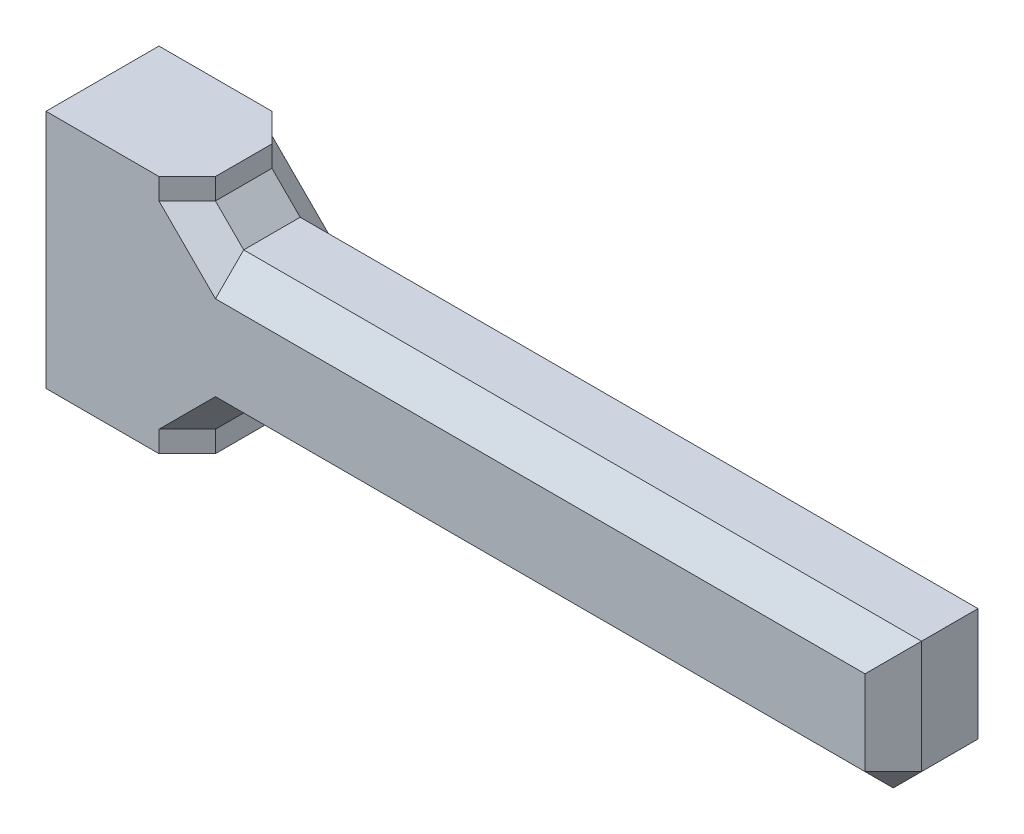
SolidWorks part; units mm, degrees
ref_plane "Front Plane" through (0, 0, 0) normal (0, 0, 1) x (1, 0, 0)
ref_plane "Top Plane" through (0, 0, 0) normal (0, 1, 0) x (1, 0, 0)
ref_plane "Right Plane" through (0, 0, 0) normal (1, 0, 0) x (0, 0, -1)
sketch "Sketch1" plane through (0, 0, 0) normal (0, 0, 1) x (1, 0, 0)
  line L0 (0, -4.25) -> (0, -2.5)
  line L1 (0, 4.25) -> (-5, 4.25)
  line L2 (-5, 4.25) -> (-5, -4.25)
  line L3 (-5, -4.25) -> (0, -4.25)
  line L4 (0, 2.5) -> (25, 2.5)
  line L5 (25, 2.5) -> (25, -2.5)
  line L6 (25, -2.5) -> (0, -2.5)
  line L7 (-98.8559, 0) -> (131.4397, 0) construction
  line L8 (0, 57.5739) -> (0, 2.5) construction
  line L10 (0, 2.5) -> (0, 4.25)
  line L11 (0, -2.5) -> (0, -92.3668) construction
  dimension "B2" = 8.5
  dimension "k" = 5
  dimension "L" = 25
  dimension "D4" = 5
extrude "BASE" add sketch "Sketch1" along normal blind 4 contours L6 L0 L3 L2 L1 L10 L4 L5
chamfer "Chamfer1" distance 1 angle 45 14 edges at (25, 0, 0) (25, 0, 4) (0, -2.5, 2) (0, 2.5, 2) (0, 3.375, 0) (0, -3.375, 4) (25, -2.5, 2) (12.5, 2.5, 0) (25, 2.5, 2) (12.5, -2.5, 4) (0, -3.375, 0) (0, 3.375, 4) (12.5, -2.5, 0) (12.5, 2.5, 4)
sketch "Sketch2" plane through (-5, 0, 0) normal (-1, 0, 0) x (0, 0, 1)
  line L0 (-1.3127, 0) -> (5.9161, 0) construction
  line L1 (2, -4.25) -> (2, 6.0184) construction
  line L2 (4, -4.25) -> (0, -4.25) construction
  line L3 (4, 4.25) -> (4, -4.25) construction
  line L4 (0, 4.25) -> (0, -4.25) construction
  line L5 (4, 4.25) -> (0, 4.25) construction
  circle A0 centre (2.0257, 0.0359) radius 1.5
  dimension "D1" = 3
  dimension "D2" = 4.2141
  dimension "D3" = 2.0257
extrude "Cut-Extrude1" cut sketch "Sketch2" against normal blind 2.5
